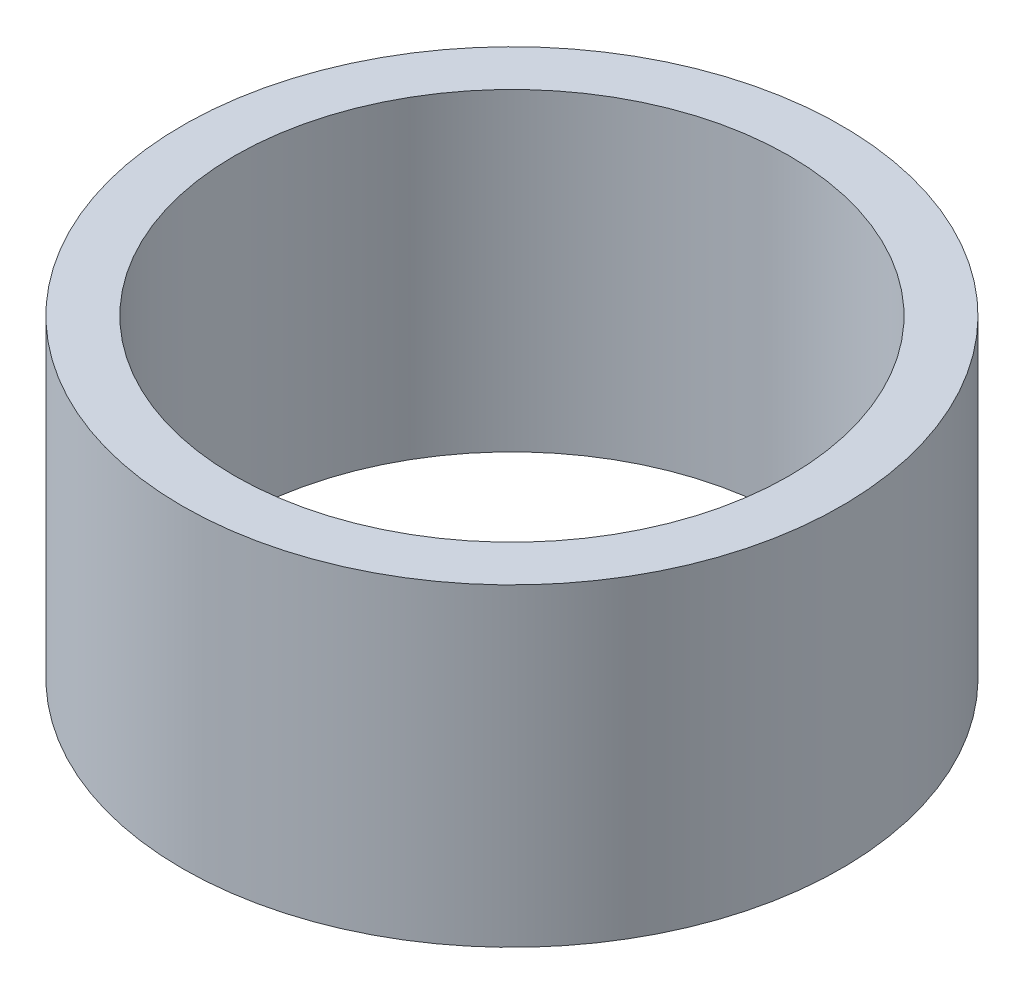
SolidWorks part; units mm, degrees
ref_plane "Front Plane" through (0, 0, 0) normal (0, 0, 1) x (1, 0, 0)
ref_plane "Top Plane" through (0, 0, 0) normal (0, 1, 0) x (1, 0, 0)
ref_plane "Right Plane" through (0, 0, 0) normal (1, 0, 0) x (0, 0, -1)
sketch "Sketch1" plane through (0, 0, 0) normal (0, 1, 0) x (1, 0, 0)
  circle A0 centre (0, 0) radius 6.3
  circle A1 centre (0, 0) radius 5.3
  dimension "D1" = 10.6
  dimension "D2" = 12.6
extrude "Boss-Extrude1" add sketch "Sketch1" along normal mid plane 6
